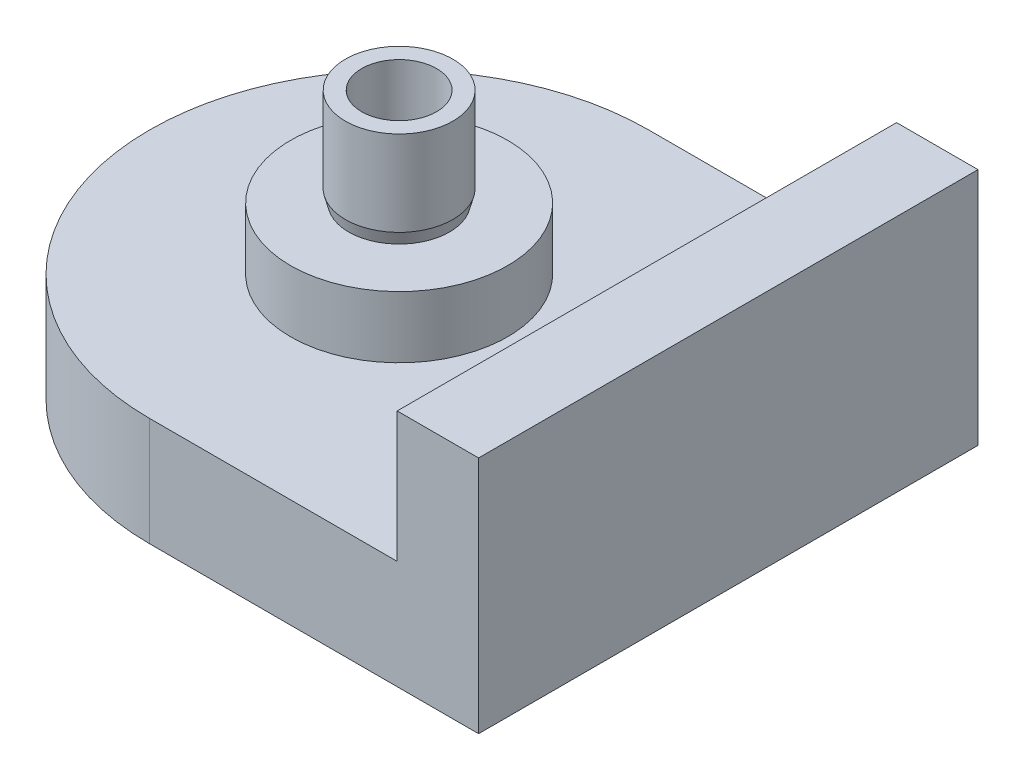
SolidWorks part; units mm, degrees
ref_plane "Front Plane" through (0, 0, 0) normal (0, 0, 1) x (1, 0, 0)
ref_plane "Top Plane" through (0, 0, 0) normal (0, 1, 0) x (1, 0, 0)
ref_plane "Right Plane" through (0, 0, 0) normal (1, 0, 0) x (0, 0, -1)
sketch "Sketch1" plane through (0, 0, 0) normal (0, 1, 0) x (1, 0, 0)
  circle A0 centre (0, 0) radius 11.5
  dimension "D1" = 23
extrude "Boss-Extrude1" add sketch "Sketch1" along normal blind 5
sketch "Sketch2" plane through (0, 5, 0) normal (0, 1, 0) x (1, 0, 0)
  circle A0 centre (0, 0) radius 5
  dimension "D1" = 10
extrude "Boss-Extrude2" add sketch "Sketch2" along normal blind 2.84
sketch "Sketch3" plane through (0, 7.84, 0) normal (0, 1, 0) x (1, 0, 0)
  circle A0 centre (0, 0) radius 2.475
  circle A1 centre (0, 0) radius 1.725
  dimension "D1" = 4.95
  dimension "D2" = 3.45
extrude "Boss-Extrude3" add sketch "Sketch3" along normal blind 4.5
sketch "Sketch4" plane through (0, 7.84, 0) normal (0, 1, 0) x (1, 0, 0)
  circle A0 centre (0, 0) radius 1.8
  dimension "D1" = 3.6
extrude "Cut-Extrude1" cut sketch "Sketch4" against normal through all
sketch "Sketch5" plane through (0, 7.84, 0) normal (0, 1, 0) x (1, 0, 0)
  circle A0 centre (0, 0) radius 2.3208
extrude "Cut-Extrude2" cut sketch "Sketch5" along normal blind 2 draft 15 flip side to cut
sketch "Sketch6" plane through (0, 0, 0) normal (0, -1, 0) x (1, 0, 0)
  line L0 (0, -10.1472) -> (0, -11.5)
  line L1 (0, 11.5) -> (15.1603, 11.5)
  line L2 (0, 11.5) -> (0, 10.1472)
  line L3 (0, -11.5) -> (15.1603, -11.5)
  line L4 (15.1603, 11.5) -> (15.1603, -11.5)
  line L5 (11.5, 0) -> (15.1603, 0) construction
  circle A0 centre (0, 0) radius 11.5 construction
  circle A1 centre (0, 0) radius 11.5 construction
  arc A2 (0, -10.1472) -> (0, 10.1472) centre (0, 0) ccw
  point P14 (13.3301, 0)
extrude "Boss-Extrude4" add sketch "Sketch6" against normal blind 5
sketch "Sketch7" plane through (0, 5, 0) normal (0, 1, 0) x (1, 0, 0)
  line L0 (15.1603, 11.5) -> (15.1603, -11.5) construction
  line L2 (10.3103, 4) -> (11.4103, 4)
  line L3 (10.3103, 4) -> (10.3103, -4)
  line L4 (10.3103, -4) -> (11.4103, -4)
  line L5 (11.4103, 4) -> (11.4103, -4)
  circle A0 centre (0, 0) radius 10.3103
  point P7 (10.3103, 0)
  dimension "D3" = 3.75
  dimension "D1" = 1.1
  dimension "D2" = 8
extrude "Cut-Extrude3" cut sketch "Sketch7" against normal blind 10 contours L5 L2 L3 L4
sketch "Sketch10" plane through (0, 5, 0) normal (0, 1, 0) x (1, 0, 0)
  line L0 (15.1603, -11.5) -> (0, -11.5) construction
  line L1 (15.1603, 11.5) -> (11.4103, 11.5)
  line L2 (15.1603, 11.5) -> (15.1603, -11.5)
  line L3 (15.1603, -11.5) -> (11.4103, -11.5)
  line L4 (11.4103, 11.5) -> (11.4103, -11.5)
  line L5 (11.4103, 4) -> (11.4103, -4) construction
extrude "Boss-Extrude5" add sketch "Sketch10" along normal blind 6
